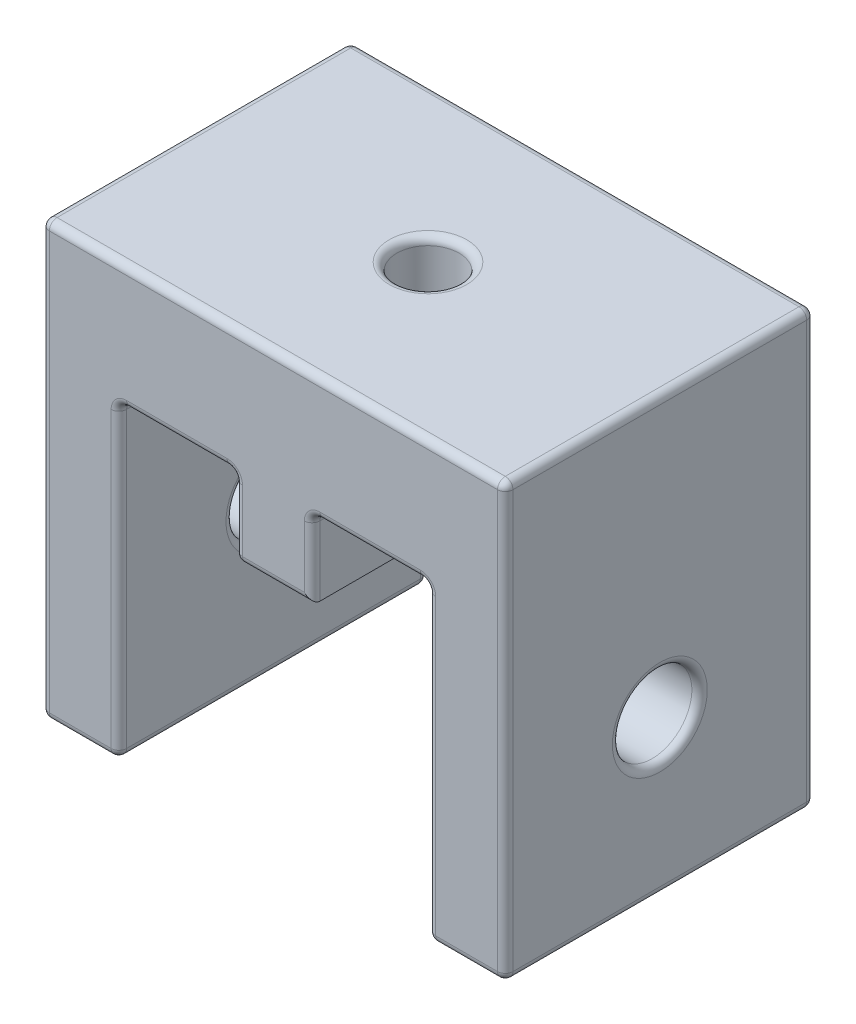
SolidWorks part; units mm, degrees
ref_plane "Front Plane" through (0, 0, 0) normal (0, 0, 1) x (1, 0, 0)
ref_plane "Top Plane" through (0, 0, 0) normal (0, 1, 0) x (1, 0, 0)
ref_plane "Right Plane" through (0, 0, 0) normal (1, 0, 0) x (0, 0, -1)
sketch "Sketch1" plane through (0, 0, 0) normal (0, 0, 1) x (1, 0, 0)
  line L0 (0, 0) -> (6.35, 0) construction
  line L1 (0, 0) -> (6.35, 0)
  line L2 (0, 0) -> (0, 35.56)
  line L3 (0, 35.56) -> (38.1, 35.56)
  line L4 (38.1, 0) -> (38.1, 35.56)
  line L5 (6.35, 0) -> (6.35, 25.4) construction
  line L6 (6.35, 25.4) -> (31.75, 25.4) construction
  line L7 (31.75, 25.4) -> (31.75, 0) construction
  line L8 (31.75, 0) -> (38.1, 0) construction
  line L9 (6.35, 0) -> (6.35, 25.4)
  line L10 (6.35, 25.4) -> (31.75, 25.4)
  line L11 (31.75, 25.4) -> (31.75, 0)
  line L12 (31.75, 0) -> (38.1, 0)
  dimension "D1" = 6.35
  dimension "D2" = 6.35
  dimension "D3" = 25.4
  dimension "D4" = 38.1
  dimension "D5" = 35.56
  dimension "D6" = 25.4
extrude "Boss-Extrude1" add sketch "Sketch1" along normal blind 25.4
sketch "Sketch2" plane through (0, 25.4, 0) normal (0, -1, 0) x (1, 0, 0)
  line L0 (0, 0) -> (19.05, 0) construction
  line L1 (6.35, 0) -> (31.75, 0) construction
  line L2 (19.05, 0) -> (19.05, 3.81) construction
  line L4 (22.225, 7.62) -> (15.875, 7.62)
  line L5 (22.225, 7.62) -> (22.225, 0)
  line L6 (22.225, 0) -> (15.875, 0)
  line L7 (15.875, 7.62) -> (15.875, 0)
  line L8 (22.225, 7.62) -> (15.875, 0) construction
  line L9 (22.225, 0) -> (15.875, 7.62) construction
  dimension "D1" = 6.35
  dimension "D2" = 7.62
extrude "Boss-Extrude2" add sketch "Sketch2" along normal blind 6.35
ref_plane "Plane1" through (0, 0, 12.7) normal (0, 0, 1) x (1, 0, 0)
mirror "Mirror1" about plane through (0, 0, 12.7) normal (0, 0, 1) of "Boss-Extrude2"
hole_wizard "1/4-20 Tapped Hole1" positions "Sketch4" profile "Sketch3" tap size "1/4-20" standard "Ansi Inch" end condition through all
sketch "Sketch4" plane through (0, 35.56, 0) normal (0, 1, 0) x (-1, 0, 0)
  line L0 (-38.1, 0) -> (0, 0) construction
  line L1 (0, 25.4) -> (0, 0) construction
  point P0 (-19.05, 12.7)
  point P2 (-19.05, 0)
  dimension "D1" = 12.7
  dimension "D2" = 19.05
sketch "Sketch3" plane through (19.05, 35.56, 12.7) normal (1, 0, 0) x (0, 0, 1)
  line L0 (0, 0) -> (0, 35.56)
  line L1 (0, 35.56) -> (2.5527, 35.56)
  line L2 (2.5527, 35.56) -> (2.5527, 0)
  line L5 (2.5527, 0) -> (0, 0)
  line L11 (0, -6.35) -> (0, 107.95) construction
  dimension "Thru Tap Drill Dia." = 5.1054
  dimension "Thru Tap Drill Depth" = 35.56
cosmetic thread "Hole Thread1" parameters "D2"=6.35
hole_wizard "#97 (0.0059) Diameter Hole1" positions "Sketch6" profile "Sketch5" hole size "#97" standard "Ansi Inch"
sketch "Sketch6" plane through (6.35, 0, 0) normal (1, 0, 0) x (0, 0, -1)
  line L0 (0, 0) -> (0, 25.4) construction
  line L1 (-25.4, 25.4) -> (0, 25.4) construction
  point P0 (-12.7, 12.7)
  dimension "D1" = 12.7
  dimension "D2" = 12.7
sketch "Sketch5" plane through (6.35, 12.7, 12.7) normal (0, 1, 0) x (0, 0, -1)
  line L0 (0, 0) -> (0, 6.35)
  line L1 (0, 6.35) -> (3.2639, 6.35)
  line L2 (3.2639, 6.35) -> (3.2639, 0)
  line L5 (3.2639, 0) -> (0, 0)
  line L11 (0, -6.35) -> (0, 107.95) construction
  dimension "Thru Hole Dia." = 6.5278
  dimension "Thru Hole Depth" = 6.35
hole_wizard "#97 (0.0059) Diameter Hole2" positions "Sketch8" profile "Sketch7" hole size "#97" standard "Ansi Inch" end condition through all
sketch "Sketch8" plane through (31.75, 0, 0) normal (-1, 0, 0) x (0, 0, 1)
  line L0 (25.4, 25.4) -> (0, 25.4) construction
  line L1 (0, 25.4) -> (0, 0) construction
  point P0 (12.7, 12.7)
  dimension "D1" = 12.7
  dimension "D2" = 12.7
sketch "Sketch7" plane through (31.75, 12.7, 12.7) normal (0, 1, 0) x (0, 0, 1)
  line L0 (0, 0) -> (0, 6.35)
  line L1 (0, 6.35) -> (3.2639, 6.35)
  line L2 (3.2639, 6.35) -> (3.2639, 0)
  line L5 (3.2639, 0) -> (0, 0)
  line L11 (0, -6.35) -> (0, 107.95) construction
  dimension "Thru Hole Dia." = 6.5278
  dimension "Thru Hole Depth" = 6.35
fillet "Fillet2" radius 0.635 53 edges at (31.75, 0, 12.7) (31.75, 12.7, 15.9639) (6.35, 0, 12.7) (6.35, 12.7, 9.4361) (22.225, 25.4, 21.59) (31.75, 25.4, 12.7) (22.225, 25.4, 3.81) (19.05, 25.4, 7.62) (15.875, 25.4, 3.81) (6.35, 25.4, 12.7) (15.875, 25.4, 21.59) (19.05, 25.4, 17.78) (19.05, 25.4, 15.2527) (34.925, 0, 25.4) (31.75, 12.7, 25.4) (26.9875, 25.4, 25.4) (22.225, 22.225, 25.4) (22.225, 22.225, 17.78) (19.05, 19.05, 17.78) (19.05, 19.05, 25.4) (15.875, 22.225, 17.78) (15.875, 22.225, 25.4) (11.1125, 25.4, 25.4) (6.35, 12.7, 25.4) (3.175, 0, 25.4) (3.175, 0, 0) (6.35, 12.7, 0) (11.1125, 25.4, 0) (15.875, 22.225, 0) (19.05, 19.05, 0) (22.225, 22.225, 0) (26.9875, 25.4, 0) (31.75, 12.7, 0) (34.925, 0, 0) (0, 17.78, 25.4) (0, 0, 12.7) (0, 17.78, 0) (0, 12.7, 9.4361) (38.1, 0, 12.7) (38.1, 17.78, 25.4) (38.1, 17.78, 0) (38.1, 12.7, 15.9639) (38.1, 35.56, 12.7) (19.05, 35.56, 25.4) (0, 35.56, 12.7) (19.05, 35.56, 0) (19.05, 35.56, 15.2527) (22.225, 22.225, 7.62) (15.875, 22.225, 7.62) (15.875, 19.05, 3.81) (19.05, 19.05, 7.62) (22.225, 19.05, 3.81) (15.875, 19.05, 21.59)
